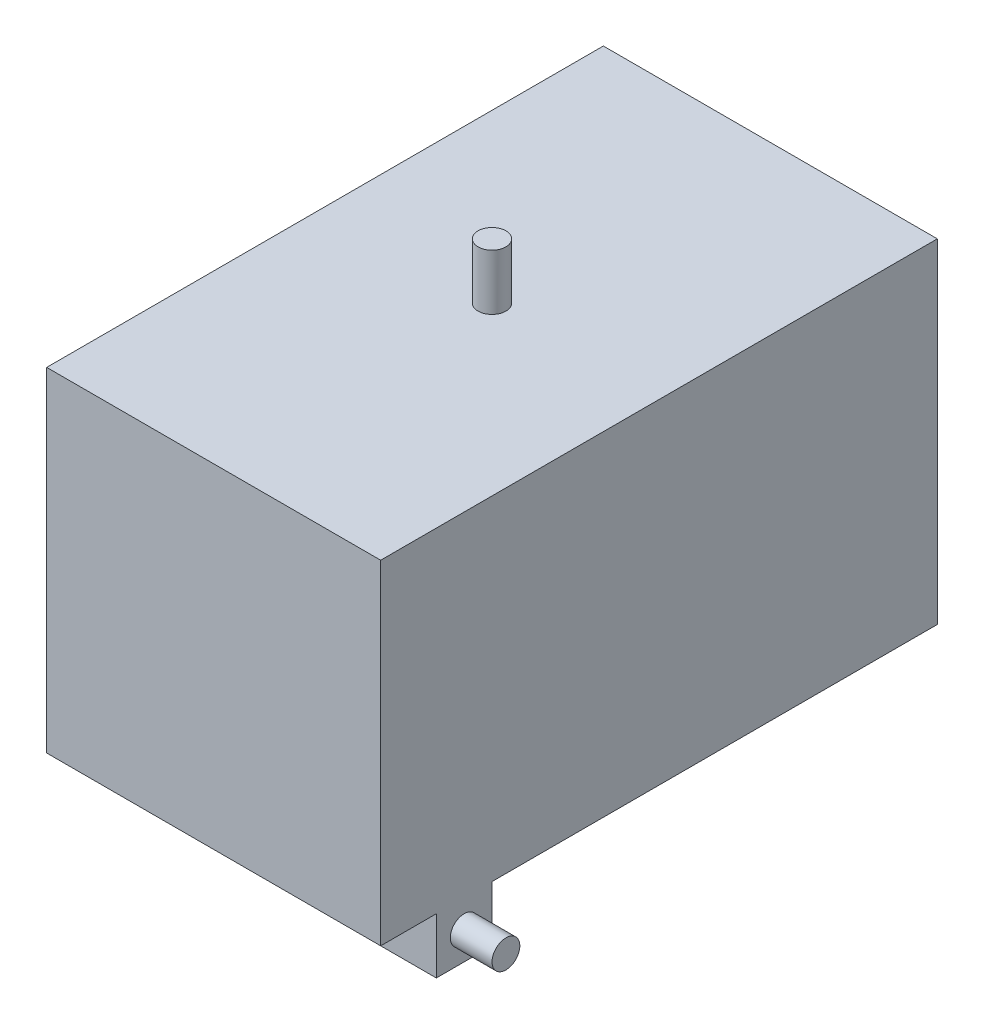
SolidWorks part; units mm, degrees
material "6061-T6 (SS)"
ref_plane "Front Plane" through (0, 0, 0) normal (0, 0, 1) x (1, 0, 0)
ref_plane "Top Plane" through (0, 0, 0) normal (0, 1, 0) x (1, 0, 0)
ref_plane "Right Plane" through (0, 0, 0) normal (1, 0, 0) x (0, 0, -1)
sketch "Sketch1" plane through (0, 0, 0) normal (0, 0, 1) x (1, 0, 0)
  line L1 (-73.025, -73.025) -> (73.025, -73.025)
  line L2 (-73.025, -73.025) -> (-73.025, 73.025)
  line L3 (-73.025, 73.025) -> (73.025, 73.025)
  line L4 (73.025, -73.025) -> (73.025, 73.025)
  line L5 (-73.025, -73.025) -> (73.025, 73.025) construction
  line L6 (-73.025, 73.025) -> (73.025, -73.025) construction
  line L7 (-76.2, -76.2) -> (76.2, -76.2)
  line L8 (-76.2, -76.2) -> (-76.2, 76.2)
  line L9 (-76.2, 76.2) -> (76.2, 76.2)
  line L10 (76.2, -76.2) -> (76.2, 76.2)
  line L11 (-76.2, -76.2) -> (76.2, 76.2) construction
  line L12 (-76.2, 76.2) -> (76.2, -76.2) construction
  point P0 (0, 0)
  point P6 (0, 0)
  dimension "D1" = 3.175
  dimension "D2" = 3.175
  dimension "D3" = 152.4
extrude "Boss-Extrude1" add sketch "Sketch1" along normal mid plane 254
sketch "Sketch2" plane through (0, 0, 127) normal (0, 0, 1) x (1, 0, 0)
  line L1 (-73.025, -73.025) -> (73.025, -73.025)
  line L2 (-73.025, -73.025) -> (-73.025, 73.025)
  line L3 (-73.025, 73.025) -> (73.025, 73.025)
  line L4 (73.025, -73.025) -> (73.025, 73.025)
  line L5 (-73.025, -73.025) -> (73.025, 73.025) construction
  line L6 (-73.025, 73.025) -> (73.025, -73.025) construction
  point P0 (0, 0)
extrude "Boss-Extrude2" add sketch "Sketch2" against normal blind 3.175
sketch "Sketch3" plane through (0, 0, -127) normal (0, 0, -1) x (-1, 0, 0)
  line L1 (-73.025, -73.025) -> (73.025, -73.025)
  line L2 (-73.025, -73.025) -> (-73.025, 73.025)
  line L3 (-73.025, 73.025) -> (73.025, 73.025)
  line L4 (73.025, -73.025) -> (73.025, 73.025)
  line L5 (-73.025, -73.025) -> (73.025, 73.025) construction
  line L6 (-73.025, 73.025) -> (73.025, -73.025) construction
  point P0 (0, 0)
extrude "Boss-Extrude3" add sketch "Sketch3" against normal blind 3.175
sketch "Sketch4" plane through (0, -76.2, 0) normal (0, -1, 0) x (1, 0, 0)
  line L0 (0, -1000) -> (0, 49000) construction
  line L1 (76.2, 127) -> (76.2, -127) construction
  line L2 (25.4, 101.6) -> (76.2, 101.6)
  line L3 (25.4, 101.6) -> (25.4, 76.2)
  line L4 (25.4, 76.2) -> (76.2, 76.2)
  line L5 (76.2, 101.6) -> (76.2, 76.2)
  line L6 (25.4, 101.6) -> (76.2, 76.2) construction
  line L7 (25.4, 76.2) -> (76.2, 101.6) construction
  line L8 (-76.2, 127) -> (76.2, 127) construction
  line L9 (-25.4, 76.2) -> (-76.2, 101.6) construction
  line L10 (-25.4, 101.6) -> (-76.2, 76.2) construction
  line L11 (-76.2, 101.6) -> (-76.2, 76.2)
  line L12 (-25.4, 76.2) -> (-76.2, 76.2)
  line L13 (-25.4, 101.6) -> (-25.4, 76.2)
  line L14 (-25.4, 101.6) -> (-76.2, 101.6)
  point P1 (50.8, 88.9)
  point P16 (-50.8, 88.9)
  dimension "D1" = 25.4
  dimension "D2" = 25.4
  dimension "D3" = 50.8
extrude "Boss-Extrude4" add sketch "Sketch4" along normal blind 25.4 separate body
ref_plane "Plane1" through (0, 0, -101.6) normal (0, 0, -1) x (-1, 0, 0)
sketch "Sketch6" plane through (0, 0, -101.6) normal (0, 0, -1) x (-1, 0, 0)
  line L0 (0, -76.2) -> (0, -127)
  line L4 (76.2, -76.2) -> (-76.2, -76.2) construction
  line L5 (25.4, -101.6) -> (9.525, -101.6)
  line L6 (9.525, -101.6) -> (9.525, -76.2)
  line L7 (9.525, -76.2) -> (0, -76.2)
  line L8 (76.2, -101.6) -> (25.4, -101.6) construction
  arc A0 (0, -127) -> (25.4, -101.6) centre (0, -101.6) ccw
  dimension "D1" = 9.525
  dimension "D2" = 50.8
revolve "Revolve2" add sketch "Sketch6" angle 360 about L0
sketch "Sketch7" plane through (0, 76.2, 0) normal (0, 1, 0) x (1, 0, 0)
  line L0 (0, 127) -> (0, -127) construction
  line L1 (76.2, -127) -> (-76.2, -127) construction
  line L2 (76.2, 0) -> (-76.2, 0) construction
  line L3 (76.2, -127) -> (76.2, 127) construction
  line L4 (-76.2, -127) -> (-76.2, 127) construction
  line L5 (76.2, 127) -> (-76.2, 127) construction
  circle A0 centre (0, 0) radius 6.35
  dimension "D1" = 12.7
extrude "Boss-Extrude5" add sketch "Sketch7" along normal blind 25.4
sketch "Sketch8" plane through (76.2, 0, 0) normal (1, 0, 0) x (0, 0, -1)
  line L0 (-88.9, -101.6) -> (-88.9, -76.2) construction
  line L1 (-76.2, -101.6) -> (-101.6, -101.6) construction
  line L2 (-76.2, -76.2) -> (-101.6, -76.2) construction
  circle A0 centre (-88.9, -88.9) radius 6.35
  dimension "D1" = 12.7
extrude "Boss-Extrude6" add sketch "Sketch8" along normal blind 19.05
sketch "Sketch9" plane through (-76.2, 0, 0) normal (-1, 0, 0) x (0, 0, 1)
  line L0 (88.9, -101.6) -> (88.9, -76.2) construction
  line L1 (101.6, -101.6) -> (76.2, -101.6) construction
  line L2 (101.6, -76.2) -> (76.2, -76.2) construction
  circle A0 centre (88.9, -88.9) radius 6.35
  dimension "D1" = 12.7
extrude "Boss-Extrude7" add sketch "Sketch9" along normal blind 19.05
ref_plane "Plane2" through (0, -127, 0) normal (0, -1, 0) x (-1, 0, 0)
